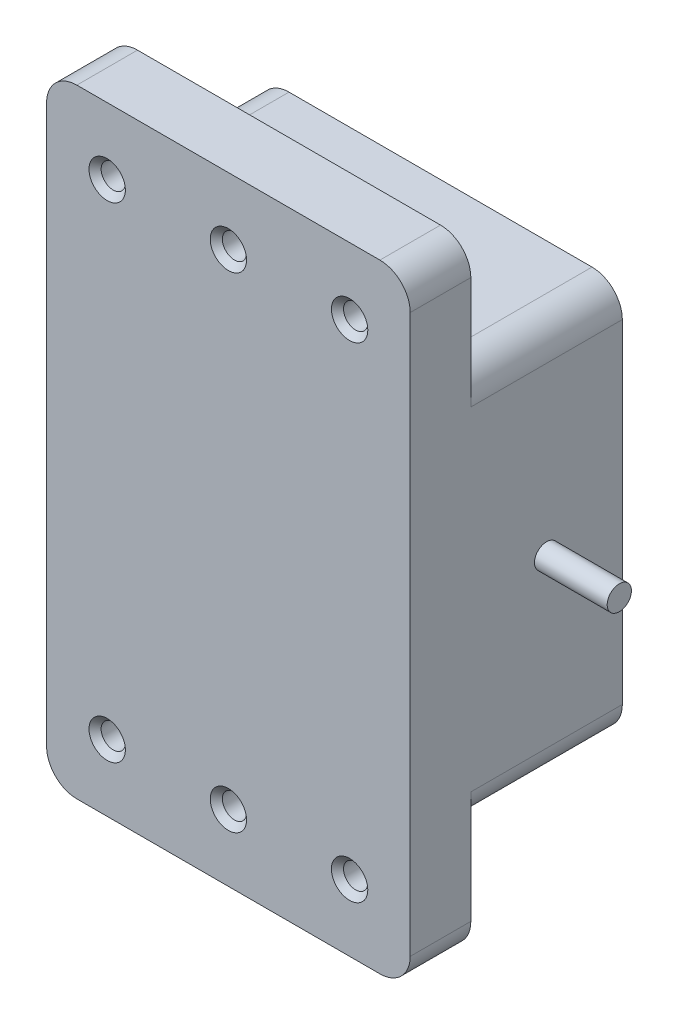
SolidWorks part; units mm, degrees
ref_plane "Front Plane" through (0, 0, 0) normal (0, 0, 1) x (1, 0, 0)
ref_plane "Top Plane" through (0, 0, 0) normal (0, 1, 0) x (1, 0, 0)
ref_plane "Right Plane" through (0, 0, 0) normal (1, 0, 0) x (0, 0, -1)
sketch "Sketch3" plane through (0, 0, 0) normal (0, 0, 1) x (1, 0, 0)
  line L0 (0, 0) -> (0, 40) construction
  line L5 (-30, 51) -> (30, 51)
  line L6 (-30, 51) -> (-30, -51)
  line L7 (-30, -51) -> (30, -51)
  line L8 (30, 51) -> (30, -51)
  line L9 (-20, 40) -> (20, 40) construction
  line L16 (-30, 0) -> (30, 0) construction
  circle A10 centre (-20, 40) radius 2
  circle A11 centre (20, 40) radius 2
  circle A12 centre (20, -40) radius 2
  circle A13 centre (-20, -40) radius 2
  circle A14 centre (0, 40) radius 2
  circle A15 centre (0, -40) radius 2
  point P0 (0, 0)
  point P10 (0, 40)
  dimension "D1" = 102
  dimension "D2" = 60
extrude "Boss-Extrude1" add sketch "Sketch3" along normal blind 10
sketch "Sketch4" plane through (0, 0, 0) normal (0, 0, -1) x (-1, 0, 0)
  line L0 (30, 51) -> (30, -51) construction
  line L1 (-30, 32.5) -> (30, 32.5)
  line L2 (-30, 32.5) -> (-30, -32.5)
  line L3 (-30, -32.5) -> (30, -32.5)
  line L4 (30, 32.5) -> (30, -32.5)
  line L5 (-30, 32.5) -> (30, -32.5) construction
  line L6 (-30, -32.5) -> (30, 32.5) construction
  point P0 (0, 0)
  dimension "D1" = 65
extrude "Boss-Extrude2" add sketch "Sketch4" along normal blind 25 contours L2 L1 L4 L3
fillet "Fillet1" radius 5 8 edges at (-30, 32.5, -12.5) (-30, -32.5, -12.5) (30, -32.5, -12.5) (30, 32.5, -12.5) (30, -51, 5) (-30, -51, 5) (30, 51, 5) (-30, 51, 5)
sketch "Sketch6" plane through (0, 0, -25) normal (0, 0, -1) x (-1, 0, 0)
  line L0 (0, 0) -> (0, -5) construction
  line L1 (-30, -5) -> (30, -5) construction
  line L2 (-30, 27.5) -> (-30, -27.5) construction
  line L3 (30, 27.5) -> (30, -27.5) construction
  text T0 "<b>MLA-30+</b>" font "Century Gothic" height 10
extrude "Cut-Extrude1" cut sketch "Sketch6" against normal blind 2
sketch "Sketch7" plane through (30, 0, 0) normal (1, 0, 0) x (0, 0, -1)
  line L0 (-10, 0) -> (25, -0.0982) construction
  line L1 (-10, -46) -> (-10, 46) construction
  line L2 (12.5, 27.5) -> (12.5, -27.5) construction
  line L3 (25, 27.5) -> (0, 27.5) construction
  line L4 (0, -27.5) -> (25, -27.5) construction
  circle A0 centre (12.5, 0) radius 2
extrude "Boss-Extrude3" add sketch "Sketch7" along normal blind 12
sketch "Sketch8" plane through (-30, 0, 0) normal (-1, 0, 0) x (0, 0, 1)
  line L0 (-25, 0) -> (10, 0) construction
  line L1 (-25, 27.5) -> (-25, -27.5) construction
  line L2 (10, 46) -> (10, -46) construction
  line L3 (-12.5, 27.5) -> (-12.5, -27.5) construction
  line L4 (0, 27.5) -> (-25, 27.5) construction
  line L5 (-25, -27.5) -> (0, -27.5) construction
  circle A0 centre (-12.5, 0) radius 2
extrude "Boss-Extrude4" add sketch "Sketch8" along normal blind 12
chamfer "Chamfer2" distance 1 angle 45 6 edges at (22, 40, 10) (-18, 40, 10) (18, -40, 10) (-22, -40, 10) (2, -40, 10) (2, 40, 10)
